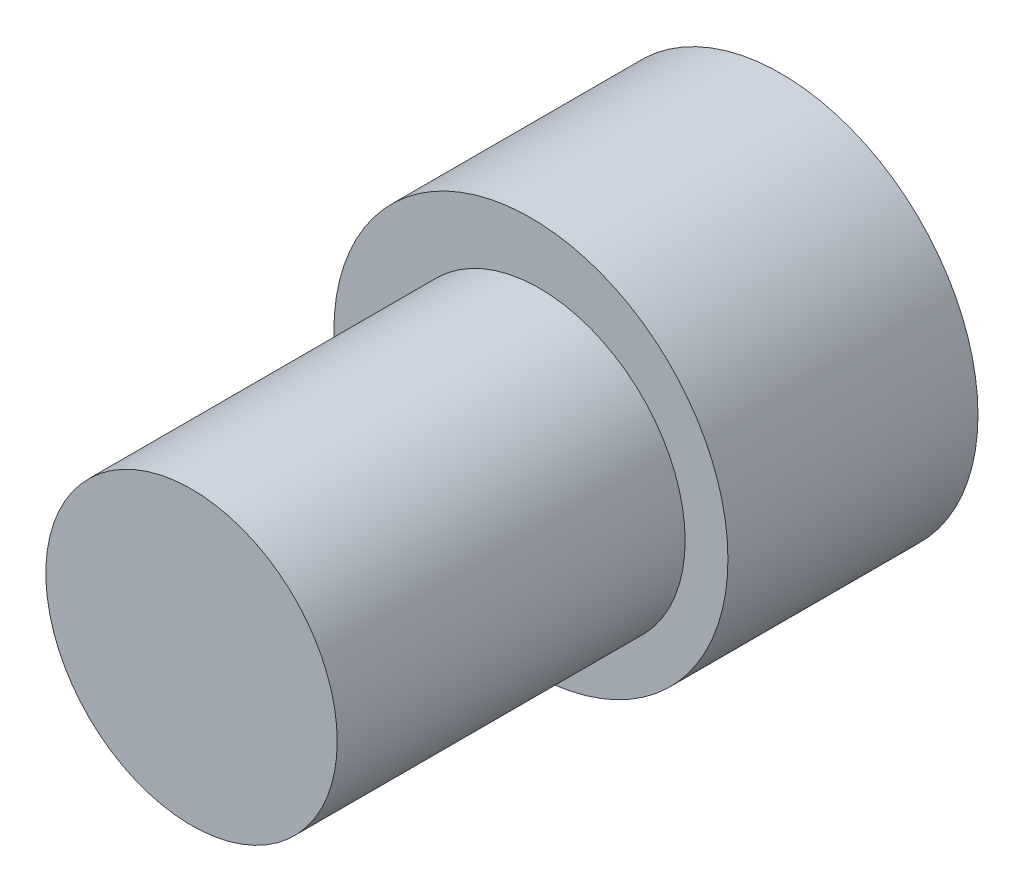
SolidWorks part; units mm, degrees
ref_plane "Front Plane" through (0, 0, 0) normal (1, 0, 0) x (0, 1, 0)
ref_plane "Top Plane" through (0, 0, 0) normal (0, 0, 1) x (0, 1, 0)
ref_plane "Right Plane" through (0, 0, 0) normal (0, 1, 0) x (-1, 0, 0)
sketch "Sketch3" plane through (0, 0, -19.2414) normal (0, 0, 1) x (1, 0, 0)
  circle A0 centre (-23.4306, 35.5721) radius 3.35
  circle A1 centre (-23.4306, 35.5721) radius 3.35
extrude "Boss-Extrude2" add sketch "Sketch3" against normal blind 8 contours A0
sketch "Sketch5" plane through (0, 0, -27.2414) normal (0, 0, -1) x (-1, 0, 0)
  circle A0 centre (-45.0571, 31.2562) radius 4
  point P2 (0, 0)
sketch "Sketch6" plane through (0, 0, -27.2414) normal (0, 0, -1) x (-1, 0, 0)
  circle A1 centre (23.6278, 35.6933) radius 4.5312
extrude "Boss-Extrude5" add sketch "Sketch6" along normal blind 5.75
